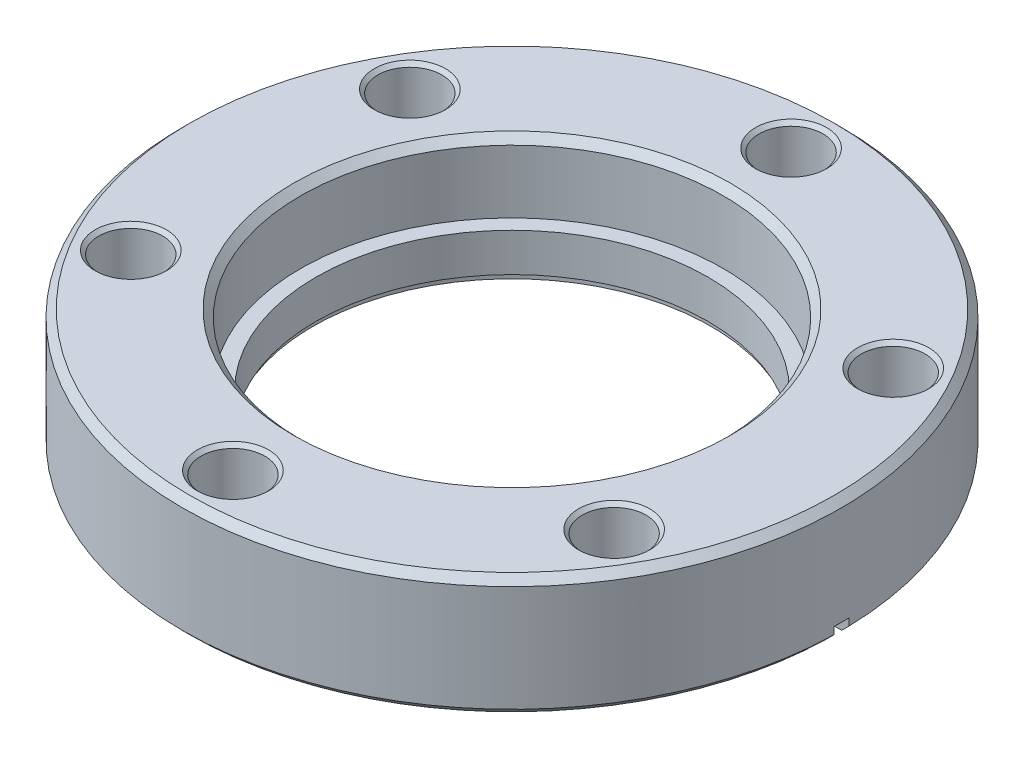
SolidWorks part; units mm, degrees
ref_plane "Front Plane" through (0, 0, 0) normal (0, 0, 1) x (1, 0, 0)
ref_plane "Top Plane" through (0, 0, 0) normal (0, 1, 0) x (1, 0, 0)
ref_plane "Right Plane" through (0, 0, 0) normal (1, 0, 0) x (0, 0, -1)
sketch "Sketch1" plane through (0, 0, 0) normal (0, 1, 0) x (1, 0, 0)
  circle A0 centre (0, 0) radius 34.671
  circle A1 centre (0, 0) radius 20.6375
  dimension "D1" = 69.342
  dimension "D2" = 41.275
extrude "Boss-Extrude1" add sketch "Sketch1" along normal blind 12.7
sketch "Sketch2" plane through (0, 12.7, 0) normal (0, 1, 0) x (1, 0, 0)
  circle A0 centre (0, 0) radius 22.225
  dimension "D1" = 44.45
extrude "Cut-Extrude1" cut sketch "Sketch2" against normal blind 7.3914
chamfer "Chamfer1" distance 0.762 angle 45 3 edges at (0, 0, 34.671) (0, 12.7, 34.671) (0, 12.7, 22.225)
sketch "Sketch3" plane through (0, 0, 0) normal (0, 0, 1) x (1, 0, 0)
  line L0 (-24.1554, 0) -> (-24.1554, 1.8252)
  line L1 (-24.1554, 1.8252) -> (-20.955, 0.6604)
  line L2 (-20.955, 0.6604) -> (-20.955, 1.27)
  line L3 (-20.955, 1.27) -> (0, 1.27)
  line L4 (-24.1554, 0) -> (0, 0)
  line L5 (0, 0) -> (0, 1.27)
  dimension "D1" = 24.1554
  dimension "D2" = 20.955
  dimension "D3" = 1.8252
  dimension "D4" = 0.6096
  dimension "D5" = 1.27
revolve "Cut-Revolve1" cut sketch "Sketch3" angle 360 about axis through (0, 12.7, 0) along (0, -1, 0)
sketch "Sketch4" plane through (0, 12.7, 0) normal (0, 1, 0) x (1, 0, 0)
  circle A0 centre (0, 29.3624) radius 3.3655
  dimension "D1" = 6.731
  dimension "D2" = 29.3624
extrude "Cut-Extrude2" cut sketch "Sketch4" against normal through all
chamfer "Chamfer2" distance 0.381 angle 45 2 edges at (0, 12.7, -25.9969) (0, 0, -25.9969)
pattern_circular "CirPattern1" count 6 every 60 about axis through (0, 0, 0) along (0, 1, 0) of "Cut-Extrude2", "Chamfer2"
sketch "Sketch5" plane through (0, 0, 0) normal (0, 0, 1) x (1, 0, 0)
  line L0 (-23.7652, 0.946) -> (-35.8694, 1.5803)
  line L1 (23.7652, 0.946) -> (23.7652, -0.2995)
  line L2 (-35.8694, 1.5803) -> (-35.8694, -0.2995)
  line L3 (-35.8694, -0.2995) -> (-23.7652, -0.2995)
  line L4 (35.8694, -0.2995) -> (23.7652, -0.2995)
  line L5 (35.8694, 1.5803) -> (35.8694, -0.2995)
  line L6 (23.7652, 0.946) -> (35.8694, 1.5803)
  line L7 (-23.7652, 0.946) -> (-23.7652, -0.2995)
  line L9 (0, -0.2995) -> (0, 0) construction
  line L10 (0, -0.2995) -> (-23.7652, 0.946) construction
  dimension "D1" = 0.2995
  dimension "D2" = 3
extrude "Cut-Extrude3" cut sketch "Sketch5" against normal mid plane 1.5875
